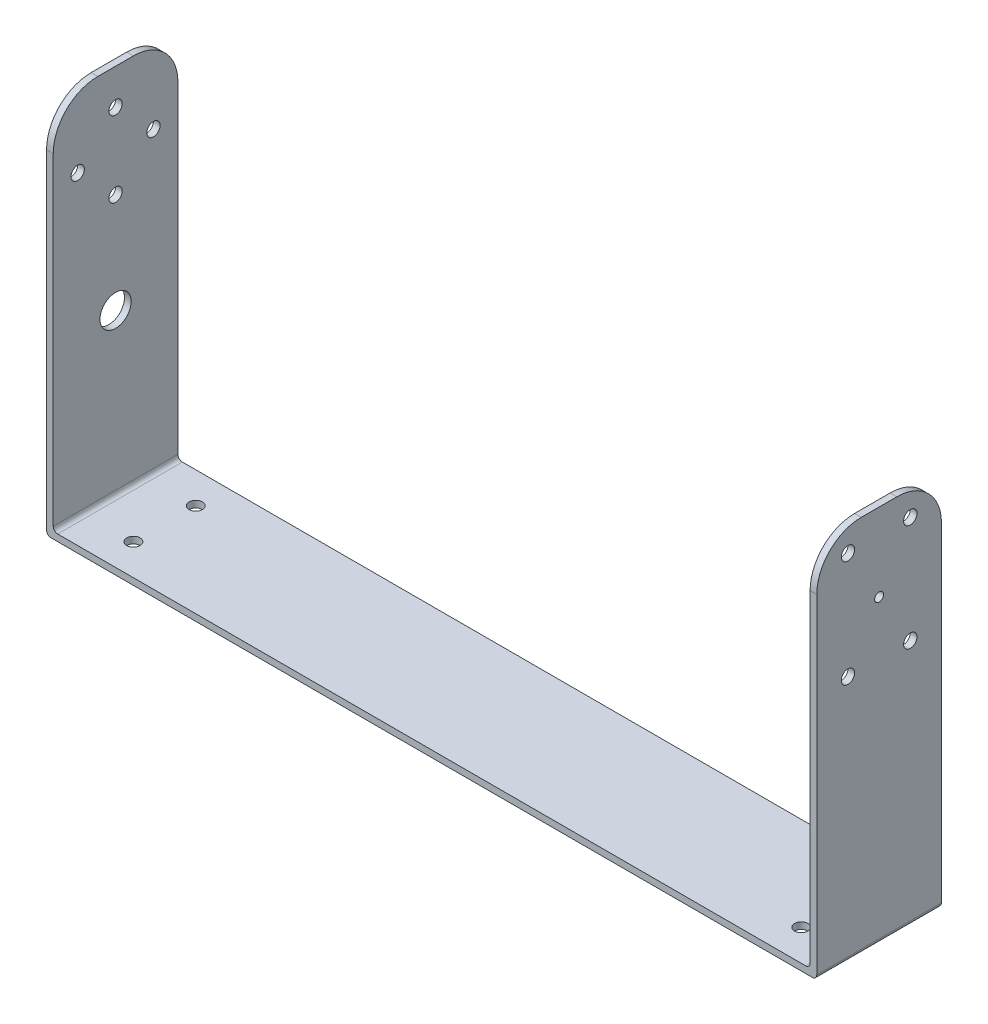
SolidWorks part; units mm, degrees
ref_plane "Front Plane" through (0, 0, 0) normal (0, 0, 1) x (1, 0, 0)
ref_plane "Top Plane" through (0, 0, 0) normal (0, 1, 0) x (1, 0, 0)
ref_plane "Right Plane" through (0, 0, 0) normal (1, 0, 0) x (0, 0, -1)
sketch "Sketch1" plane through (0, 0, 0) normal (0, 1, 0) x (1, 0, 0)
  line L1 (0, 0) -> (170, 0)
  line L2 (0, 0) -> (0, 28)
  line L3 (0, 28) -> (170, 28)
  line L4 (170, 0) -> (170, 28)
  dimension "D1" = 28
  dimension "D2" = 170
extrude "Boss-Extrude1" add sketch "Sketch1" along normal blind 1.5
sketch "Sketch2" plane through (0, 0, 0) normal (1, 0, 0) x (0, 0, -1)
  line L1 (28, 0) -> (0, 0)
  line L2 (28, 0) -> (28, 85)
  line L3 (28, 85) -> (0, 85)
  line L4 (0, 0) -> (0, 85)
  dimension "D1" = 85
extrude "Boss-Extrude2" add sketch "Sketch2" against normal blind 1.5
fillet "Fillet2" radius 10 2 edges at (-0.75, 85, -28) (-0.75, 85, 0)
fillet "Fillet3" radius 1 1 edges at (-1.5, 0, -14)
fillet "Fillet4" radius 1 1 edges
sketch "Sketch5" plane through (0, 0, 0) normal (1, 0, 0) x (0, 0, -1)
  line L0 (18, 85) -> (10, 85) construction
  line L1 (0, 75) -> (0, 2.5) construction
  line L2 (28, 2.5) -> (28, 75) construction
  circle A0 centre (14, 77) radius 1.5
  circle A1 centre (14, 60) radius 1.5
  circle A2 centre (22.5, 68.5) radius 1.5
  circle A3 centre (5.5, 68.5) radius 1.5
  point P8 (14, 85)
  dimension "D1" = 8
  dimension "D2" = 14
  dimension "D3" = 17
  dimension "D4" = 14
  dimension "D7" = 5.5
  dimension "D8" = 16.5
  dimension "D9" = 16.5
  dimension "D10" = 5.5
extrude "Cut-Extrude2" cut sketch "Sketch5" against normal blind 15 and the other way blind 15
sketch "Sketch7" plane through (0, 0, 0) normal (1, 0, 0) x (0, 0, -1)
  circle A0 centre (14, 37.5) radius 3.5
extrude "Cut-Extrude3" cut sketch "Sketch7" against normal blind 15 and the other way blind 15
sketch "Sketch8" plane through (0, 1.5, 0) normal (0, 1, 0) x (1, 0, 0)
  line L0 (1, 28) -> (1, 0) construction
  line L2 (170, 28) -> (1, 28) construction
  line L3 (1, 0) -> (170, 0) construction
  circle A1 centre (161, 7) radius 1.5
  circle A2 centre (11, 21) radius 1.5
  circle A3 centre (11, 7) radius 1.5
  circle A4 centre (161, 21) radius 1.5
  dimension "D3" = 7
  dimension "D4" = 7
  dimension "D1" = 7
  dimension "D2" = 7
  dimension "D5" = 150
  dimension "D6" = 10
  dimension "D7" = 14
  dimension "D8" = 150
  dimension "D9" = 10
extrude "Cut-Extrude4" cut sketch "Sketch8" against normal blind 15 and the other way blind 15
sketch "Sketch11" plane through (170, 0, 0) normal (1, 0, 0) x (0, 0, -1)
  line L1 (28, 0) -> (0, 0)
  line L2 (28, 0) -> (28, 85)
  line L3 (28, 85) -> (0, 85)
  line L4 (0, 0) -> (0, 85)
  circle A0 centre (14, 67.5) radius 1
  dimension "D3" = 14
  dimension "D1" = 85
  dimension "D2" = 28
  dimension "D4" = 17.5
extrude "Boss-Extrude5" add sketch "Sketch11" along normal blind 1.5
fillet "Fillet5" radius 1 1 edges
fillet "Fillet6" radius 1 1 edges at (171.5, 0, -14)
fillet "Fillet7" radius 10 1 edges at (170.75, 85, 0)
fillet "Fillet8" radius 10 1 edges at (170.75, 85, -28)
sketch "Sketch12" plane through (170, 0, 0) normal (-1, 0, 0) x (0, 0, 1)
  line L4 (-28, 2.5) -> (-28, 75) construction
  line L5 (0, 75) -> (0, 2.5) construction
  circle A0 centre (-21, 79.5) radius 1.5
  circle A1 centre (-7, 79.5) radius 1.5
  circle A2 centre (-7, 55.5) radius 1.5
  circle A3 centre (-21, 55.5) radius 1.5
  circle A4 centre (-14, 67.5) radius 1 construction
  dimension "D1" = 12
  dimension "D2" = 7
  dimension "D3" = 12
  dimension "D4" = 7
  dimension "D5" = 12
  dimension "D6" = 7
  dimension "D7" = 7
  dimension "D8" = 12
extrude "Cut-Extrude5" cut sketch "Sketch12" against normal blind 10 and the other way blind 10
